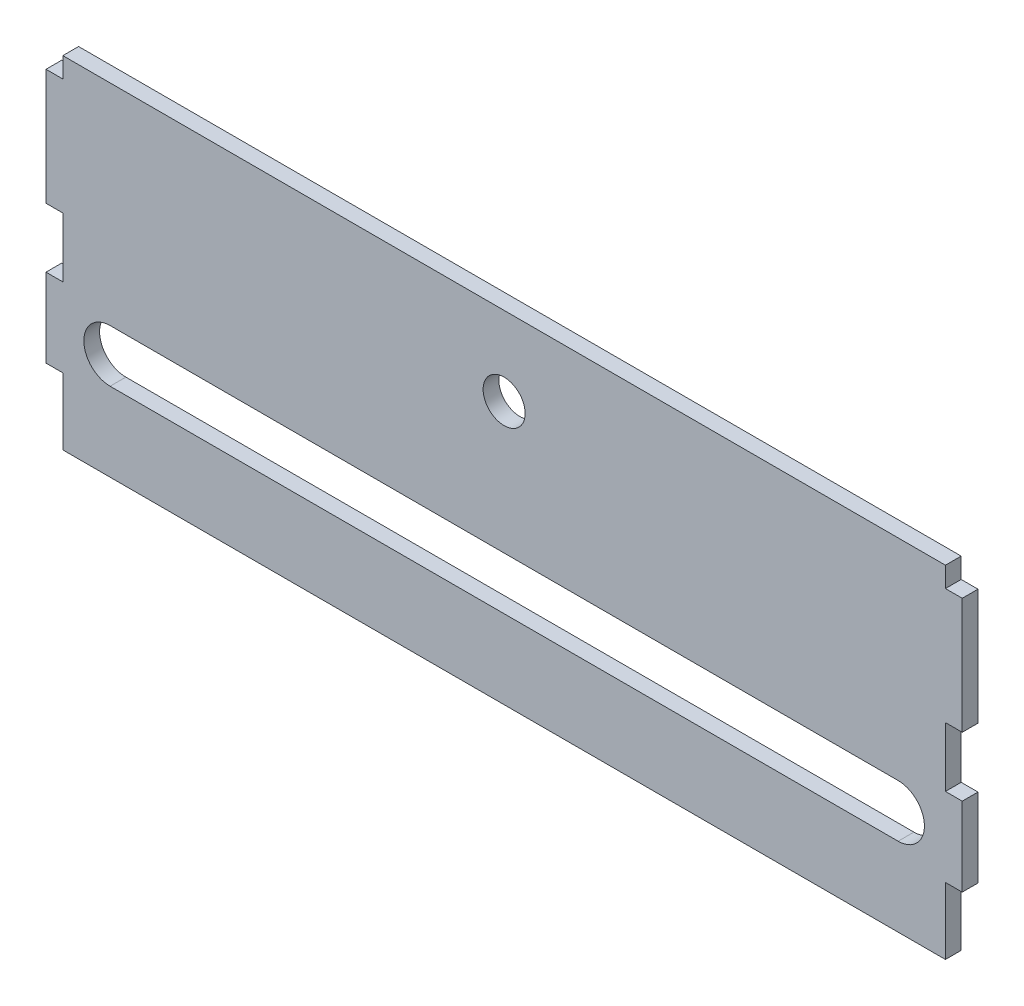
SolidWorks part; units mm, degrees
ref_plane "Alzado" through (0, 0, 0) normal (0, 0, 1) x (1, 0, 0)
ref_plane "Planta" through (0, 0, 0) normal (0, 1, 0) x (1, 0, 0)
ref_plane "Vista lateral" through (0, 0, 0) normal (1, 0, 0) x (0, 0, -1)
sketch "Croquis1" plane through (0, 0, 0) normal (0, 0, 1) x (1, 0, 0)
  line L0 (-84, 37.2954) -> (-87.2, 37.2954)
  line L1 (84, -50) -> (-84, -50)
  line L2 (84, -50) -> (84, -37.2954)
  line L3 (84, 50) -> (-84, 50)
  line L4 (-84, -50) -> (-84, -37.2954)
  line L5 (84, -50) -> (-84, 50) construction
  line L6 (84, 50) -> (-84, -50) construction
  line L7 (-87.2, 37.2954) -> (-87.2, 22.2954)
  line L8 (-87.2, 22.2954) -> (-84, 22.2954)
  line L9 (-84, 37.2954) -> (-84, 50)
  line L10 (0, 50) -> (0, -50) construction
  line L11 (-84, 0) -> (84, 0) construction
  line L12 (-87.2, -22.2954) -> (-84, -22.2954)
  line L13 (-87.2, -37.2954) -> (-87.2, -22.2954)
  line L14 (-84, -37.2954) -> (-87.2, -37.2954)
  line L15 (84, -37.2954) -> (87.2, -37.2954)
  line L16 (87.2, -37.2954) -> (87.2, -22.2954)
  line L17 (87.2, -22.2954) -> (84, -22.2954)
  line L18 (87.2, 22.2954) -> (84, 22.2954)
  line L19 (87.2, 37.2954) -> (87.2, 22.2954)
  line L20 (84, 37.2954) -> (87.2, 37.2954)
  line L21 (84, 37.2954) -> (84, 50)
  line L22 (84, -22.2954) -> (84, -10.9454)
  line L23 (-84, -22.2954) -> (-84, -10.9454)
  line L24 (-84, 11.1479) -> (-87.2, 11.1479)
  line L25 (-87.2, 11.1479) -> (-87.2, -10.9454)
  line L26 (-87.2, -10.9454) -> (-84, -10.9454)
  line L27 (-84, 11.1479) -> (-84, 22.2954)
  line L28 (87.2, -10.9454) -> (84, -10.9454)
  line L29 (87.2, 11.1479) -> (87.2, -10.9454)
  line L30 (84, 11.1479) -> (87.2, 11.1479)
  line L31 (84, 11.1479) -> (84, 22.2954)
  line L32 (-75, -30) -> (75, -30) construction
  line L33 (-75, -25) -> (75, -25)
  line L34 (-75, -35) -> (75, -35)
  line L35 (-75, 30) -> (75, 30) construction
  line L36 (-75, 25) -> (75, 25)
  line L37 (-75, 35) -> (75, 35)
  circle A0 centre (0, 0) radius 4
  arc A1 (-75, -25) -> (-75, -35) centre (-75, -30) ccw
  arc A2 (75, -35) -> (75, -25) centre (75, -30) ccw
  arc A3 (-75, 25) -> (-75, 35) centre (-75, 30) cw
  arc A4 (75, 35) -> (75, 25) centre (75, 30) cw
  point P0 (0, 0)
  point P38 (0, -30)
  point P45 (0, 30)
  dimension "D10" = 8
  dimension "D13" = 150
  dimension "D1" = 168
  dimension "D2" = 100
  dimension "D3" = 3.2
  dimension "D4" = 15
  dimension "D5" = 12.7046
  dimension "D6" = 44.5908
  dimension "D7" = 11.1475
  dimension "D8" = 11.35
  dimension "D9" = 87.2
  dimension "D11" = 10
  dimension "D12" = 30
  dimension "D14" = 0
extrude "Saliente-Extruir1" add sketch "Croquis1" along normal blind 3
sketch "Croquis2" plane through (0, 0, 3) normal (0, 0, 1) x (1, 0, 0)
  line L1 (-92.3955, 15) -> (91.2665, 15)
  line L2 (-92.3955, 15) -> (-92.3955, 50)
  line L3 (-92.3955, 50) -> (91.2665, 50)
  line L4 (91.2665, 15) -> (91.2665, 50)
  line L6 (84, 50) -> (-84, 50) construction
  dimension "D1" = 0
  dimension "D2" = 35
extrude "Cortar-Extruir1" cut sketch "Croquis2" against normal through all
